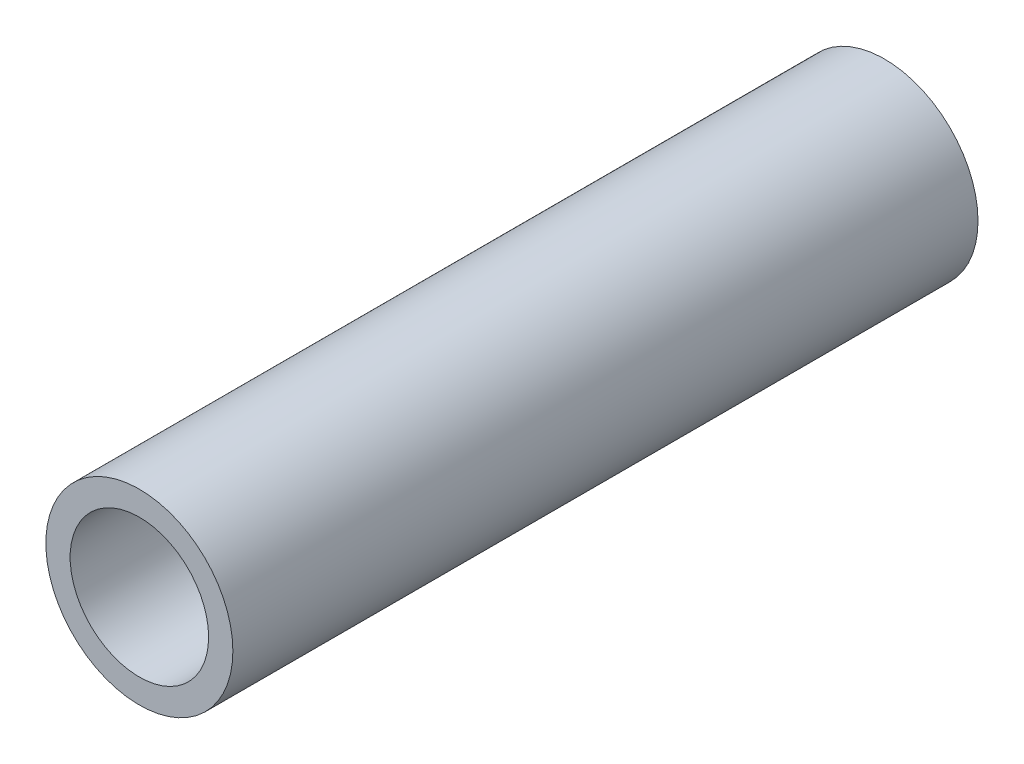
SolidWorks part; units mm, degrees
ref_plane "Front Plane" through (0, 0, 0) normal (0, 0, 1) x (1, 0, 0)
ref_plane "Top Plane" through (0, 0, 0) normal (0, 1, 0) x (1, 0, 0)
ref_plane "Right Plane" through (0, 0, 0) normal (1, 0, 0) x (0, 0, -1)
sketch "Sketch1" plane through (0, 0, 0) normal (0, 0, 1) x (1, 0, 0)
  circle A0 centre (0, 0) radius 10.668
  dimension "Pipe OD" = 21.336
extrude "Extrude-Thin1" add sketch "Sketch1" along normal mid plane 85 thin thin type one direction reverse wall 2.7686
